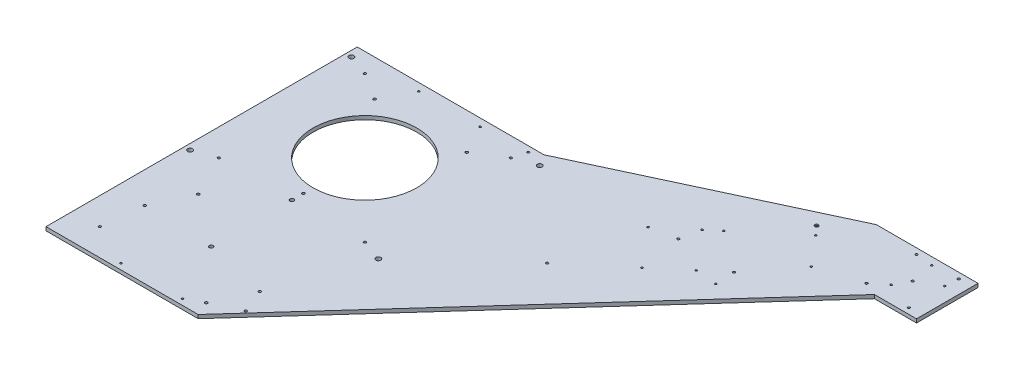
SolidWorks part; units mm, degrees
ref_plane "Front Plane" through (0, 0, 0) normal (0, 0, 1) x (1, 0, 0)
ref_plane "Top Plane" through (0, 0, 0) normal (0, 1, 0) x (1, 0, 0)
ref_plane "Right Plane" through (0, 0, 0) normal (1, 0, 0) x (0, 0, -1)
sketch "Sketch1" plane through (0, 0, 0) normal (0, 1, 0) x (1, 0, 0)
  line L0 (-260, 240) -> (226, 240)
  line L1 (226, 240) -> (816, 515.1)
  line L2 (816, 515.1) -> (1080.6, 515.1)
  line L3 (1080.6, 515.1) -> (1080.6, 355.1)
  line L4 (1080.6, 355.1) -> (971, 355.1)
  line L5 (971, 355.1) -> (136, -570)
  line L6 (136, -570) -> (-260, -570)
  line L7 (-260, -570) -> (-260, 240)
  dimension "D1" = 260
  dimension "D2" = 570
  dimension "D3" = 240
  dimension "D4" = 226
  dimension "D5" = 136
  dimension "D6" = 355.1
  dimension "D7" = 971
  dimension "D8" = 1080.6
  dimension "D9" = 816
  dimension "D10" = 515.1
extrude "Plate Outlite - Boss-Extrude" add sketch "Sketch1" along normal blind 9.53
sketch "Sketch2" plane through (0, 9.53, 0) normal (0, 1, 0) x (1, 0, 0)
  circle A0 centre (0, 0) radius 135
  dimension "D1" = 270
extrude "Beam Clearance Hole" cut sketch "Sketch2" against normal up to next
sketch "Sketch3" plane through (0, 9.53, 0) normal (0, 1, 0) x (1, 0, 0)
  point P0 (-190, 190)
  point P1 (-190, -500)
  point P3 (190, -500)
  point P5 (190, 190)
  point P6 (190, -190)
  point P7 (-190, -190)
  dimension "D1" = 190
  dimension "D2" = 190
  dimension "D5" = 500
  dimension "D3" = 2
  dimension "D4" = 2
hole_wizard "A - Ø6.2 (6.2) Diameter Hole" positions "Sketch4" profile "Sketch5" hole size "Ø6.2" standard "ANSI Metric" end condition up to next
sketch "Sketch4" plane through (0, 9.53, 0) normal (0, 1, 0) x (1, 0, 0)
  point P0 (-190, 190)
  point P3 (190, 190)
  point P6 (190, -190)
  point P9 (-190, -190)
  point P15 (-190, -500)
  point P18 (190, -500)
sketch "Sketch5" plane through (-190, 9.53, -190) normal (1, 0, 0) x (0, 0, 1)
  line L0 (0, 0) -> (0, 9.53)
  line L1 (0, 9.53) -> (3.1, 9.53)
  line L2 (3.1, 9.53) -> (3.1, 0)
  line L5 (3.1, 0) -> (0, 0)
  line L11 (0, -6.35) -> (0, 107.95) construction
  dimension "Thru Hole Dia." = 6.2
  dimension "Thru Hole Depth" = 9.53
hole_wizard "B - Tap Drill for M6x1.0 Tap" positions "Sketch6" profile "Sketch7" hole size "M6x1.0" standard "ANSI Metric" end condition up to next
sketch "Sketch6" plane through (0, 9.53, 0) normal (0, 1, 0) x (1, 0, 0)
  point P0 (-80, 220)
  point P2 (80, 220)
  point P4 (524.5, 212.5)
  point P6 (979.9, 495.2)
  point P8 (1043.4, 465.7)
  point P10 (971, 398.8)
  point P12 (761.6, 412)
  point P14 (826.04, 335.57)
  point P16 (684.8, 177.3)
  point P18 (601, 276.7)
  point P20 (608.3, 112.8)
  point P22 (80, -555)
  point P24 (-80, -555)
  point P26 (740.8, 172.5)
  point P28 (631.6, 302.5)
  dimension "D1" = 80
  dimension "D2" = 80
  dimension "D3" = 80
  dimension "D4" = 80
  dimension "D5" = 220
  dimension "D6" = 220
  dimension "D7" = 555
  dimension "D8" = 555
  dimension "D9" = 524.5
  dimension "D10" = 212.5
  dimension "D11" = 276.7
  dimension "D12" = 601
  dimension "D13" = 631.6
  dimension "D14" = 302.5
  dimension "D15" = 761.6
  dimension "D16" = 412
  dimension "D17" = 979.9
  dimension "D18" = 495.2
  dimension "D19" = 1043.4
  dimension "D20" = 465.7
  dimension "D21" = 971
  dimension "D22" = 826.04
  dimension "D23" = 398.8
  dimension "D24" = 335.57
  dimension "D25" = 177.3
  dimension "D26" = 172.5
  dimension "D27" = 112.8
  dimension "D28" = 740.8
  dimension "D29" = 684.8
  dimension "D30" = 608.3
sketch "Sketch7" plane through (-80, 9.53, -220) normal (1, 0, 0) x (0, 0, 1)
  line L0 (0, 0) -> (0, 9.53)
  line L1 (0, 9.53) -> (2.5, 9.53)
  line L2 (2.5, 9.53) -> (2.5, 0)
  line L5 (2.5, 0) -> (0, 0)
  line L11 (0, -6.35) -> (0, 107.95) construction
  dimension "Thru Hole Dia." = 5
  dimension "Thru Hole Depth" = 9.53
hole_wizard "C - Ø12.5 (12.5) Diameter Hole" positions "Sketch8" profile "Sketch9" hole size "Ø12.5" standard "ANSI Metric" end condition up to next
sketch "Sketch8" plane through (0, 9.53, 0) normal (0, 1, 0) x (1, 0, 0)
  point P0 (-245, 210)
  point P2 (-245, -210)
  point P4 (245, -210)
  point P6 (245, 210)
  dimension "D1" = 210
  dimension "D2" = 245
  dimension "D3" = 245
  dimension "D4" = 210
  dimension "D5" = 245
  dimension "D6" = 210
  dimension "D7" = 245
  dimension "D8" = 210
sketch "Sketch9" plane through (-245, 9.53, -210) normal (1, 0, 0) x (0, 0, 1)
  line L0 (0, 0) -> (0, 9.53)
  line L1 (0, 9.53) -> (6.35, 9.53)
  line L2 (6.35, 9.53) -> (6.35, 0)
  line L5 (6.35, 0) -> (0, 0)
  line L11 (0, -6.35) -> (0, 107.95) construction
  dimension "Thru Hole Dia." = 12.7
  dimension "Thru Hole Depth" = 9.53
hole_wizard "E - Ø6.2 (6.2) Diameter Hole" positions "Sketch10" profile "Sketch11" hole size "Ø6.2" standard "ANSI Metric" end condition up to next
sketch "Sketch10" plane through (0, 9.53, 0) normal (0, 1, 0) x (1, 0, 0)
  point P0 (935.6, 500.1)
  point P2 (1045.6, 500.1)
  point P4 (1045.6, 370.1)
  point P6 (935.6, 370.1)
  dimension "D1" = 935.6
  dimension "D2" = 1045.6
  dimension "D3" = 500.1
  dimension "D4" = 370.1
sketch "Sketch11" plane through (935.6, 9.53, -500.1) normal (1, 0, 0) x (0, 0, 1)
  line L0 (0, 0) -> (0, 9.53)
  line L1 (0, 9.53) -> (3.1, 9.53)
  line L2 (3.1, 9.53) -> (3.1, 0)
  line L5 (3.1, 0) -> (0, 0)
  line L11 (0, -6.35) -> (0, 107.95) construction
  dimension "Thru Hole Dia." = 6.2
  dimension "Thru Hole Depth" = 9.53
hole_wizard "F - Tap Drill for M8x1.25 Tap" positions "Sketch12" profile "Sketch13" hole size "M8x1.25" standard "ANSI Metric" end condition up to next
sketch "Sketch12" plane through (0, 9.53, 0) normal (0, 1, 0) x (1, 0, 0)
  point P0 (-120, 145)
  point P2 (120, 145)
  point P4 (0, -160)
  point P6 (-134.9, -298.7)
  point P8 (-179.1, -393.9)
  point P10 (120.1, -533)
  point P12 (164.4, -437.8)
  dimension "D1" = 145
  dimension "D2" = 120
  dimension "D3" = 120
  dimension "D4" = 160
  dimension "D5" = 298.7
  dimension "D6" = 393.9
  dimension "D7" = 437.8
  dimension "D8" = 533
  dimension "D9" = 134.9
  dimension "D10" = 179.1
  dimension "D11" = 164.4
  dimension "D12" = 120.1
sketch "Sketch13" plane through (-120, 9.53, -145) normal (1, 0, 0) x (0, 0, 1)
  line L0 (0, 0) -> (0, 9.53)
  line L1 (0, 9.53) -> (3.4, 9.53)
  line L2 (3.4, 9.53) -> (3.4, 0)
  line L5 (3.4, 0) -> (0, 0)
  line L11 (0, -6.35) -> (0, 107.95) construction
  dimension "Thru Hole Dia." = 6.8
  dimension "Thru Hole Depth" = 9.53
hole_wizard "J - Ø6.0 (6) Diameter Hole" positions "Sketch14" profile "Sketch15" hole size "Ø6.0" standard "ANSI Metric" end condition up to next
sketch "Sketch14" plane through (0, 9.53, 0) normal (0, 1, 0) x (1, 0, 0)
  point P0 (200, 225.1)
  point P2 (474.5, 0)
  point P4 (738.3, 222.4)
  point P6 (590.6, 225.1)
  dimension "D1" = 225.1
  dimension "D2" = 200
  dimension "D3" = 474.5
  dimension "D4" = 590.6
  dimension "D5" = 225.1
  dimension "D6" = 222.4
  dimension "D7" = 738.3
sketch "Sketch15" plane through (200, 9.53, -225.1) normal (1, 0, 0) x (0, 0, 1)
  line L0 (0, 0) -> (0, 9.53)
  line L1 (0, 9.53) -> (3, 9.53)
  line L2 (3, 9.53) -> (3, 0)
  line L5 (3, 0) -> (0, 0)
  line L11 (0, -6.35) -> (0, 107.95) construction
  dimension "Thru Hole Dia." = 6
  dimension "Thru Hole Depth" = 9.53
hole_wizard "K - Ø10.0 (10) Diameter Hole" positions "Sketch16" profile "Sketch17" hole size "Ø10.0" standard "ANSI Metric" end condition up to next
sketch "Sketch16" plane through (0, 9.53, 0) normal (0, 1, 0) x (1, 0, 0)
  point P0 (0, -190)
  point P2 (0, -400)
  dimension "D1" = 400
  dimension "D2" = 190
sketch "Sketch17" plane through (0, 9.53, 190) normal (1, 0, 0) x (0, 0, 1)
  line L0 (0, 0) -> (0, 9.53)
  line L1 (0, 9.53) -> (5, 9.53)
  line L2 (5, 9.53) -> (5, 0)
  line L5 (5, 0) -> (0, 0)
  line L11 (0, -6.35) -> (0, 107.95) construction
  dimension "Thru Hole Dia." = 10
  dimension "Thru Hole Depth" = 9.53
hole_wizard "L - 6.1mm Hole, 9.53mm C-bore 3.2mm deep" positions "Sketch18" profile "Sketch19" legacy end condition up to next
sketch "Sketch18" plane through (0, 9.53, 0) normal (0, 1, 0) x (1, 0, 0)
  point P0 (740.6, 435.1)
  dimension "D1" = 740.6
  dimension "D2" = 435.1
sketch "Sketch19" plane through (740.6, 9.53, -435.1) normal (1, 0, 0) x (0, 0, 1)
  line L0 (0, 0) -> (0, 11.3626)
  line L1 (0, 11.3626) -> (3.05, 9.53)
  line L2 (3.05, 9.53) -> (3.05, 3.2)
  line L3 (3.05, 3.2) -> (4.765, 3.2)
  line L4 (4.765, 0) -> (0, 0)
  line L5 (0, -11.3109) -> (0, 121.1557) construction
  line L6 (0, 11.3626) -> (-3.05, 9.53) construction
  line L7 (4.765, 3.2) -> (4.765, 0)
  dimension "Depth" = 9.53
  dimension "Drill Angle" = 118
  dimension "Diameter" = 6.1
  dimension "C-Bore Diameter" = 9.53
  dimension "C-Bore Depth" = 3.2
hole_wizard "M - Ø6.0 (6) Diameter Hole" positions "Sketch20" profile "Sketch21" hole size "Ø6.0" standard "ANSI Metric"
sketch "Sketch20" plane through (0, 9.53, 0) normal (0, 1, 0) x (1, 0, 0)
  point P0 (990.6, 435.1)
  dimension "D1" = 990.6
  dimension "D2" = 435.1
sketch "Sketch21" plane through (990.6, 9.53, -435.1) normal (1, 0, 0) x (0, 0, 1)
  line L0 (0, 0) -> (0, 11.8026)
  line L1 (0, 11.8026) -> (3, 10)
  line L2 (3, 10) -> (3, 0)
  line L5 (3, 0) -> (0, 0)
  line L10 (0, 11.8026) -> (-3, 10) construction
  line L11 (0, -6.35) -> (0, 107.95) construction
  dimension "Hole Dia." = 6
  dimension "Hole Depth" = 10
  dimension "Drill Angle" = 118
